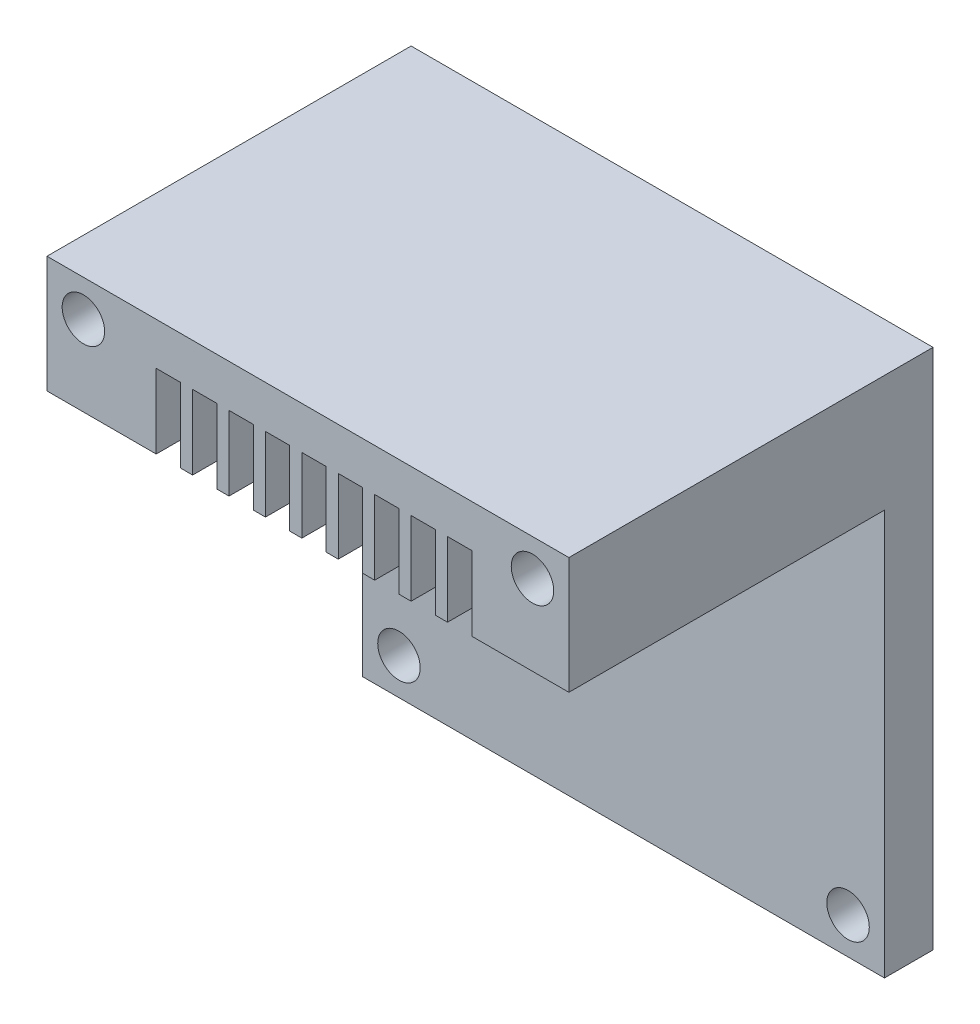
SolidWorks part; units mm, degrees
material "Thornel VCB-20 碳布"
ref_plane "前视基准面" through (0, 0, 0) normal (0, 0, 1) x (1, 0, 0)
ref_plane "上视基准面" through (0, 0, 0) normal (0, 1, 0) x (1, 0, 0)
ref_plane "右视基准面" through (0, 0, 0) normal (1, 0, 0) x (0, 0, -1)
sketch "草图1" plane through (0, 0, 0) normal (0, 0, 1) x (1, 0, 0)
  line L1 (-21.5, 21.5) -> (21.5, 21.5)
  line L2 (-21.5, 21.5) -> (-21.5, -21.5)
  line L3 (-21.5, -21.5) -> (21.5, -21.5)
  line L4 (21.5, 21.5) -> (21.5, -21.5)
  line L5 (0, -21.5) -> (0, 21.5) construction
  line L6 (-21.5, 0) -> (21.5, 0) construction
  circle A0 centre (-18.5, 18.5) radius 1.75
  circle A1 centre (-18.5, -18.5) radius 1.75
  circle A2 centre (18.5, -18.5) radius 1.75
  circle A3 centre (18.5, 18.5) radius 1.75
  point P0 (0, 0)
  dimension "D3" = 37
  dimension "D4" = 37
  dimension "D5" = 3.5
  dimension "D1" = 43
  dimension "D2" = 43
extrude "凸台-拉伸1" add sketch "草图1" along normal blind 30
sketch "草图2" plane through (0, 0, 30) normal (0, 0, 1) x (1, 0, 0)
  line L0 (-21.5, 11.8846) -> (21.5, 11.8846)
  line L4 (21.5, -21.5) -> (21.5, 21.5)
  line L5 (21.5, 21.5) -> (-21.5, 21.5)
  line L6 (-21.5, 21.5) -> (-21.5, -21.5)
  line L7 (-21.5, -21.5) -> (21.5, -21.5)
  line L8 (21.5, -21.5) -> (21.5, 21.5)
  line L9 (21.5, 21.5) -> (-21.5, 21.5)
  line L10 (-21.5, 21.5) -> (-21.5, -21.5)
  line L11 (-21.5, -21.5) -> (21.5, -21.5)
  circle M5 centre (18.5, -18.5) radius 1.75
  line M7 (21.5, -21.5) -> (21.5, 21.5)
  line M9 (-21.5, 21.5) -> (-21.5, -21.5)
  line M10 (-21.5, -21.5) -> (21.5, -21.5)
  circle M11 centre (-18.5, -18.5) radius 1.75
  dimension "D1" = 0
extrude "切除-拉伸1" cut sketch "草图2" against normal blind 26 contours L0 M9 M10 M7 M11 M5
sketch "草图3" plane through (0, 0, 30) normal (0, 0, 1) x (1, 0, 0)
  line L0 (-15.5, 11.8846) -> (-15.5, 18)
  line L1 (-15.5, 18) -> (-13.5, 18)
  line L2 (-13.5, 18) -> (-13.5, 11.8846)
  line L3 (-12.5, 11.8846) -> (-12.5, 18)
  line L4 (-21.5, 21.5) -> (-21.5, 11.8846)
  line L5 (-21.5, 11.8846) -> (21.5, 11.8846)
  line L6 (21.5, 11.8846) -> (21.5, 21.5)
  line L7 (21.5, 21.5) -> (-21.5, 21.5)
  line L8 (-21.5, 21.5) -> (-21.5, 11.8846)
  line L9 (-21.5, 11.8846) -> (21.5, 11.8846)
  line L10 (21.5, 11.8846) -> (21.5, 21.5)
  line L11 (21.5, 21.5) -> (-21.5, 21.5)
  line L12 (-12.5, 18) -> (-10.5, 18)
  line L13 (-10.5, 18) -> (-10.5, 11.8846)
  line L14 (-9.5, 11.8846) -> (-9.5, 18)
  line L15 (-9.5, 18) -> (-7.5, 18)
  line L16 (-7.5, 18) -> (-7.5, 11.8846)
  line L17 (-6.5, 11.8846) -> (-6.5, 18)
  line L18 (-6.5, 18) -> (-4.5, 18)
  line L19 (-4.5, 18) -> (-4.5, 11.8846)
  line L20 (-3.5, 11.8846) -> (-3.5, 18)
  line L21 (-3.5, 18) -> (-1.5, 18)
  line L22 (-1.5, 18) -> (-1.5, 11.8846)
  line L23 (-0.5, 11.8846) -> (-0.5, 18)
  line L24 (-0.5, 18) -> (1.5, 18)
  line L25 (1.5, 18) -> (1.5, 11.8846)
  line L26 (2.5, 11.8846) -> (2.5, 18)
  line L27 (2.5, 18) -> (4.5, 18)
  line L28 (4.5, 18) -> (4.5, 11.8846)
  line L29 (5.5, 11.8846) -> (5.5, 18)
  line L30 (5.5, 18) -> (7.5, 18)
  line L31 (7.5, 18) -> (7.5, 11.8846)
  line L32 (8.5, 11.8846) -> (8.5, 18)
  line L33 (8.5, 18) -> (10.5, 18)
  line L34 (10.5, 18) -> (10.5, 11.8846)
  line L35 (11.5, 11.8846) -> (11.5, 18)
  line L36 (11.5, 18) -> (13.5, 18)
  line L37 (13.5, 18) -> (13.5, 11.8846)
  line M10 (-21.5, 11.8846) -> (21.5, 11.8846)
  dimension "D2" = 2
  dimension "D3" = 6
  dimension "D4" = 3.5
  dimension "D1" = 0
  dimension "D5" = 10
extrude "切除-拉伸2" cut sketch "草图3" against normal blind 26 contours L13 L12 L3 M10 | L16 L15 L14 M10 | L19 L18 L17 M10 | L22 L21 L20 M10 | L25 L24 L23 M10 | L28 L27 L26 M10 | L31 L30 L29 M10 | L34 L33 L32 M10 | L37 L36 L35 M10
